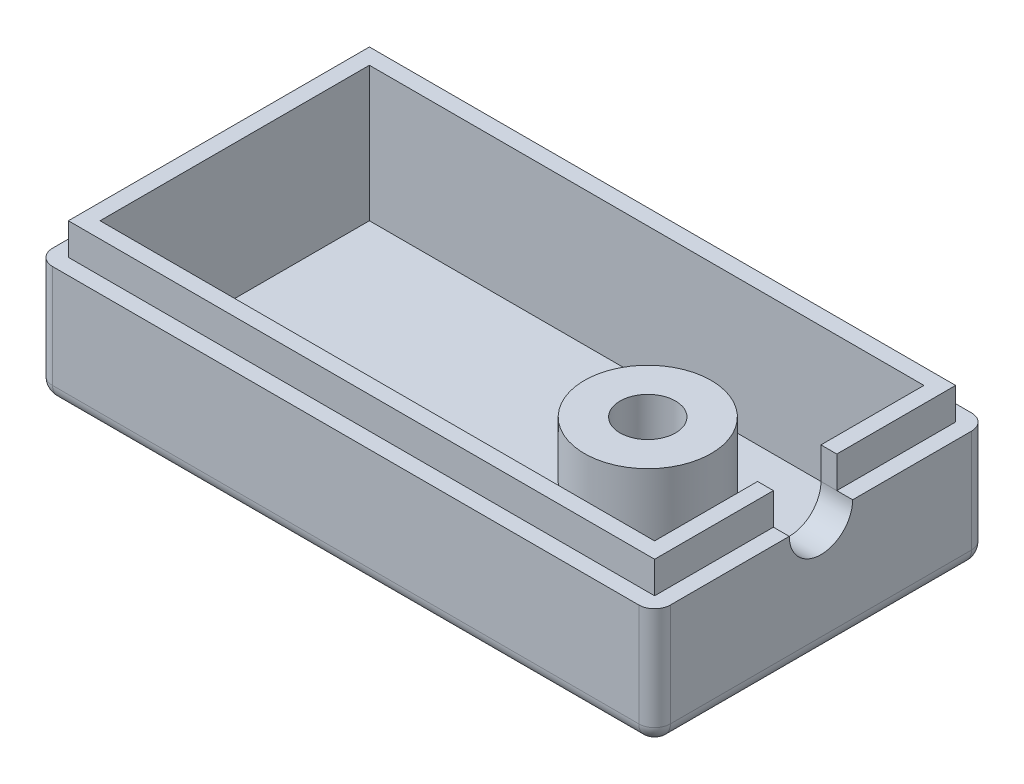
SolidWorks part; units mm, degrees
ref_plane "Front Plane" through (0, 0, 0) normal (0, 0, 1) x (1, 0, 0)
ref_plane "Top Plane" through (0, 0, 0) normal (0, 1, 0) x (1, 0, 0)
ref_plane "Right Plane" through (0, 0, 0) normal (1, 0, 0) x (0, 0, -1)
sketch "Sketch1" plane through (0, 0, 0) normal (0, 1, 0) x (1, 0, 0)
  line L1 (0, 0) -> (39, 0)
  line L2 (0, 0) -> (0, 21)
  line L3 (0, 21) -> (39, 21)
  line L4 (39, 0) -> (39, 21)
  dimension "D1" = 39
  dimension "D2" = 21
extrude "Boss-Extrude1" add sketch "Sketch1" along normal blind 7.5
sketch "Sketch2" plane through (0, 7.5, 0) normal (0, 1, 0) x (1, 0, 0)
  line L8 (1, 20) -> (1, 1)
  line L9 (1, 1) -> (38, 1)
  line L10 (38, 1) -> (38, 20)
  line L11 (38, 20) -> (1, 20)
  line L12 (1, 20) -> (1, 1)
  line L13 (1, 1) -> (38, 1)
  line L14 (38, 1) -> (38, 20)
  line L15 (38, 20) -> (1, 20)
  dimension "D1" = 1
extrude "Cut-Extrude1" cut sketch "Sketch2" against normal offset from surface (6.5 mm away) 1 up to face at (19.5, 0, -10.5)
fillet "Fillet1" radius 1 4 edges at (39, 3.75, 0) (39, 3.75, -21) (0, 3.75, -21) (0, 3.75, 0)
fillet "Fillet2" radius 1 8 edges at (0.2929, 0, -0.2929) (19.5, 0, 0) (38.7071, 0, -0.2929) (0, 0, -10.5) (0.2929, 0, -20.7071) (39, 0, -10.5) (38.7071, 0, -20.7071) (19.5, 0, -21)
sketch "Sketch3" plane through (0, 1, 0) normal (0, 1, 0) x (1, 0, 0)
  line L8 (38, 20) -> (1, 20)
  line L9 (1, 20) -> (1, 1)
  line L10 (1, 1) -> (38, 1)
  line L11 (38, 1) -> (38, 20)
  line L16 (38, 20) -> (1, 20)
  line L17 (1, 20) -> (1, 1)
  line L18 (1, 1) -> (38, 1)
  line L19 (38, 1) -> (38, 20)
  dimension "D1" = 0
extrude "Boss-Extrude2" add sketch "Sketch3" along normal blind 8.5
sketch "Sketch4" plane through (0, 9.5, 0) normal (0, 1, 0) x (1, 0, 0)
  line L8 (37, 2) -> (37, 19)
  line L9 (37, 19) -> (2, 19)
  line L10 (2, 19) -> (2, 2)
  line L11 (2, 2) -> (37, 2)
  line L12 (37, 2) -> (37, 19)
  line L13 (37, 19) -> (2, 19)
  line L14 (2, 19) -> (2, 2)
  line L15 (2, 2) -> (37, 2)
  dimension "D1" = 1
extrude "Cut-Extrude2" cut sketch "Sketch4" against normal blind 8.5
sketch "Sketch5" plane through (0, 1, 0) normal (0, 1, 0) x (1, 0, 0)
  line L0 (2, 19) -> (2, 2) construction
  line L1 (37, 19) -> (2, 19) construction
  line L2 (2, 2) -> (37, 2) construction
  line L3 (1, 20) -> (38, 20) construction
  line L4 (38, 1) -> (1, 1) construction
  line L5 (1, 1) -> (1, 20) construction
  line L6 (38, 20) -> (38, 1) construction
  circle A0 centre (28.01, 10.56) radius 4
  point P4 (0, 0)
  dimension "D4" = 8
  dimension "D1" = 26.01
  dimension "D2" = 8.44
  dimension "D3" = 8.56
  dimension "D5" = 9.44
  dimension "D6" = 9.56
  dimension "D7" = 27.01
  dimension "D8" = 9.99
extrude "Boss-Extrude3" add sketch "Sketch5" along normal up to surface (6.5 mm away) up to face at (19.5, 7.5, -10.5)
sketch "Sketch6" plane through (0, 7.5, 0) normal (0, 1, 0) x (1, 0, 0)
  circle A2 centre (28.01, 10.56) radius 3
  circle A3 centre (28.01, 10.56) radius 3
  dimension "D1" = 1
extrude "Cut-Extrude3" cut sketch "Sketch6" against normal up to surface (7.5 mm away) up to face at (19.5, 0, -10.5)
sketch "Sketch7" plane through (0, 7.5, 0) normal (0, 1, 0) x (1, 0, 0)
  circle A1 centre (28.01, 10.56) radius 4
  circle A2 centre (28.01, 10.56) radius 4
  dimension "D1" = 0
extrude "Boss-Extrude4" add sketch "Sketch7" against normal blind 4
sketch "Sketch8" plane through (0, 7.5, 0) normal (0, 1, 0) x (1, 0, 0)
  circle A0 centre (28.01, 10.56) radius 1.75
  dimension "D1" = 3.5
extrude "Cut-Extrude4" cut sketch "Sketch8" against normal up to surface (4 mm away) up to face at (28.01, 3.5, -7.56)
sketch "Sketch9" plane through (39, 0, 0) normal (1, 0, 0) x (0, 0, -1)
  line L0 (1, 7.5) -> (20, 7.5) construction
  line L1 (8.5, 7.5) -> (8.5, 9.5)
  line L2 (1, 9.5) -> (20, 9.5) construction
  line L3 (8.5, 9.5) -> (12.5, 9.5)
  line L4 (12.5, 9.5) -> (12.5, 7.5)
  arc A0 (8.5, 7.5) -> (12.5, 7.5) centre (10.5, 7.5) ccw
  dimension "D1" = 4
extrude "Cut-Extrude5" cut sketch "Sketch9" against normal up to surface (2 mm away) up to face at (37, 5.25, -10.5)
